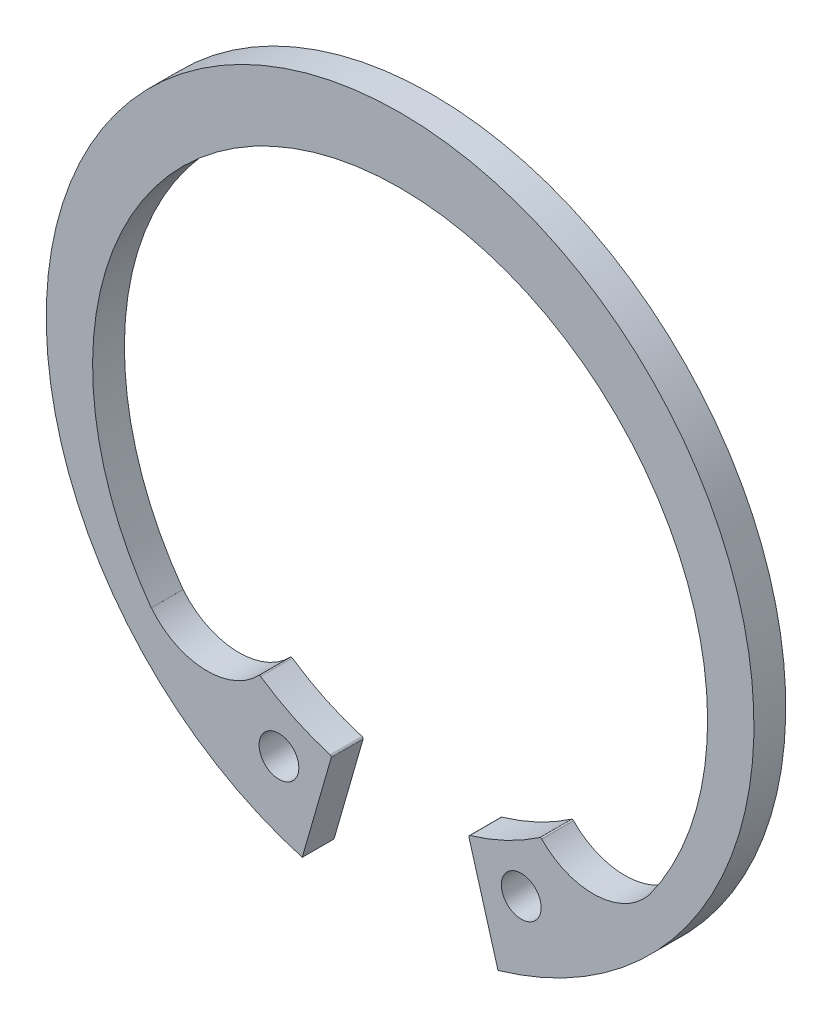
SolidWorks part; units mm, degrees
ref_plane "Plane1" through (0, 0, 0) normal (0, 0, 1) x (1, 0, 0)
ref_plane "Plane2" through (0, 0, 0) normal (0, 1, 0) x (1, 0, 0)
ref_plane "Plane3" through (0, 0, 0) normal (1, 0, 0) x (0, 0, -1)
extrude "Body" add sketch "BodySke" against normal blind 2
sketch "BodySke" plane through (0, 0, 0) normal (0, 0, 1) x (1, 0, 0)
  line L0 (-1.5431, 0) -> (1.5431, 0) construction
  line L1 (0, 0) -> (0, 18.15) construction
  line L2 (6.1547, -21.3818) -> (4.9987, -17.3656)
  line L3 (-6.1547, -21.3818) -> (-4.9987, -17.3656)
  line L4 (0, 0) -> (14.8837, -16.539) construction
  line L5 (0, 0) -> (-14.8837, -16.539) construction
  line L6 (-7.2716, -15.4106) -> (-7.9631, -17.813) construction
  line L7 (7.4097, -15.8905) -> (7.825, -17.3331) construction
  arc A0 (-4.9987, -17.3656) -> (-9.6525, -14.7997) centre (-7.6173, -16.6118) ccw
  arc A1 (9.6525, -14.7997) -> (4.9987, -17.3656) centre (7.6173, -16.6118) ccw
  arc A2 (13.5123, -15.0152) -> (-13.5123, -15.0152) centre (0, -1.1852) ccw construction
  arc A3 (6.1547, -21.3818) -> (-6.1547, -21.3818) centre (0, 0) ccw
  circle A4 centre (7.6173, -16.6118) radius 1.25
  circle A5 centre (-7.6173, -16.6118) radius 1.25
  circle A6 centre (7.6173, -16.6118) radius 2.725 construction
  arc A7 (13.6052, -14.9239) -> (-13.6052, -14.9239) centre (0, -1.1852) ccw
  arc A8 (-7.6173, -16.6118) -> (7.6173, -16.6118) centre (0, 0) ccw construction
  arc A9 (-13.6052, -14.9239) -> (-9.6525, -14.7997) centre (-11.6877, -12.9877) ccw
  arc A10 (9.6525, -14.7997) -> (13.6052, -14.9239) centre (11.6877, -12.9877) ccw
  dimension "GrooveDia" = 44.5
  dimension "TipRad" = 2.725
  dimension "HoleOffsetRad" = 18.275
  dimension "HoleDia" = 2.5
  dimension "FilletRad" = 2.725
  dimension "LargeRad" = 18.15
  dimension "SmallRad" = 20.2
  dimension "SmallAngle" = 83.969
  dimension "GapAngle" = 32.117
sketch "Clipboard" plane through (0, 0, 0) normal (0, 0, 1) x (1, 0, 0)
  line L0 (0, 0) -> (4.1, 0)
  line L1 (0, 0) -> (0, 2.05)
  line L2 (0, 0) -> (0, -6.7)
  circle A0 centre (0, 0) radius 1.25
  circle A1 centre (0, 0) radius 21
  dimension "HoleDia" = 2.5
  dimension "BoreDia" = 42
  dimension "LargeSection" = 4.1
  dimension "SmallSection" = 2.05
  dimension "LugSection" = 6.7
sketch "ModLugSke" plane through (0, 0, 0) normal (0, 0, 1) x (1, 0, 0)
  line L0 (6.1547, -21.3818) -> (4.329, -15.039)
  line L1 (-6.1547, -21.3818) -> (-4.329, -15.039)
  line L2 (12.1328, -9.7262) -> (17.3604, -13.9169) construction
  line L3 (-12.1328, -9.7262) -> (-17.3604, -13.9169) construction
  line L4 (-6.1547, -21.3818) -> (-4.9987, -17.3656) construction
  line L5 (4.9987, -17.3656) -> (6.1547, -21.3818) construction
  line L6 (0, 0) -> (0, -18.0732) construction
  line L7 (15.6421, -12.5394) -> (17.3604, -13.9169)
  line L8 (-17.3604, -13.9169) -> (-15.6421, -12.5394)
  arc A0 (6.1547, -21.3818) -> (17.3604, -13.9169) centre (0, 0) ccw
  arc A1 (-8.7715, -12.8399) -> (-4.3968, -14.9155) centre (0, 0) ccw
  arc A2 (6.1547, -21.3818) -> (-6.1547, -21.3818) centre (0, 0) ccw construction
  arc A3 (9.6525, -14.7997) -> (4.9987, -17.3656) centre (7.6173, -16.6118) ccw construction
  arc A4 (-8.7715, -12.8399) -> (-8.8997, -12.853) centre (-8.8279, -12.9225) ccw
  arc A5 (-15.6421, -12.5394) -> (-8.8997, -12.853) centre (-12.1328, -9.7262) ccw
  arc A6 (13.6052, -14.9239) -> (-13.6052, -14.9239) centre (0, -1.1852) ccw construction
  arc A7 (8.8997, -12.853) -> (15.6421, -12.5394) centre (12.1328, -9.7262) ccw
  arc A8 (4.3968, -14.9155) -> (8.7715, -12.8399) centre (0, 0) ccw
  arc A9 (-17.3604, -13.9169) -> (-6.1547, -21.3818) centre (0, 0) ccw
  circle A10 centre (-7.6173, -16.6118) radius 1.25
  circle A11 centre (-7.6173, -16.6118) radius 1.25 construction
  circle A12 centre (7.6173, -16.6118) radius 1.25
  circle A13 centre (7.6173, -16.6118) radius 1.25 construction
  arc A14 (-4.3968, -14.9155) -> (-4.329, -15.039) centre (-4.4251, -15.0114) cw
  arc A15 (4.3968, -14.9155) -> (4.329, -15.039) centre (4.4251, -15.0114) ccw
  arc A16 (8.7715, -12.8399) -> (8.8997, -12.853) centre (8.8279, -12.9225) cw
  point P43 (4.3014, -14.9432)
  dimension "D1" = 0.1
  dimension "LugAng" = 68.677
extrude "ModLug" add sketch "ModLugSke" against normal through all
sketch "UnlSke" [suppressed] plane through (0, 0, 0) normal (0, 0, 1) x (1, 0, 0)
  line L0 (1.9946, -7.8506) -> (3.2259, -12.6966)
  line L1 (-1.9946, -7.8506) -> (-3.2259, -12.6966)
  line L2 (-3.2259, -12.6966) -> (-2.0191, -7.9469) construction
  line L3 (2.0191, -7.9469) -> (3.2259, -12.6966) construction
  arc A0 (1.9946, -7.8506) -> (-1.9946, -7.8506) centre (0, 0) ccw
  arc A1 (3.2259, -12.6966) -> (-3.2259, -12.6966) centre (0, 0) ccw
  arc A2 (3.2259, -12.6966) -> (-3.2259, -12.6966) centre (0, 0) ccw construction
  circle A4 centre (-4.6101, -9.2107) radius 1
  circle A5 centre (4.6101, -9.2107) radius 1
  circle A6 centre (4.6101, -9.2107) radius 1 construction
  circle A7 centre (-4.6101, -9.2107) radius 1 construction
  arc A8 (2.0902, -7.8257) -> (4.8943, -6.4541) centre (0, 0) ccw construction
extrude "Unlug" [suppressed] add sketch "UnlSke" against normal through all
equation "' \"BoreDia@Clipboard\" = 20"
equation "' \"Thickness@Body\" = 1.5"
equation "' \"GrooveDia@BodySke\" = 21"
equation "' \"LugSection@Clipboard\" = 4.5"
equation "' \"LargeSection@Clipboard\" = 2.4"
equation "' \"HoleDia@Clipboard\" = 2"
equation "' \"BoreDia@Clipboard\" = 25"
equation "' \"GrooveDia@BodySke\" = 26.2"
equation "' \"LugSection@Clipboard\" = 5"
equation "' \"LargeSection@Clipboard\" = 3.1"
equation "\"SmallSection@Clipboard\" = \"LargeSection@Clipboard\" * 0.5"
equation "\"TipRad@BodySke\" = (\"LugSection@Clipboard\" - (\"GrooveDia@BodySke\" / 2  -  \"BoreDia@Clipboard\" / 2 ) ) / 2"
equation "\"HoleOffsetRad@BodySke\" = (\"GrooveDia@BodySke\" / 2) - \"LugSection@Clipboard\"  + \"TipRad@BodySke\""
equation "\"LargeRad@BodySke\" =  \"GrooveDia@BodySke\" / 2 -  \"LargeSection@Clipboard\""
equation "\"SmallRad@BodySke\" =  \"GrooveDia@BodySke\" / 2 -  \"SmallSection@Clipboard\""
equation "\"HoleDia@BodySke\" =  \"HoleDia@Clipboard\""
equation "\"FilletRad@BodySke\" = \"TipRad@BodySke\" * 1.0"
equation "\"GapAngle@BodySke\" = 360 - 0.965 * 360 * ( \"BoreDia@Clipboard\" /  \"GrooveDia@BodySke\")"
equation "\"LugAng@ModLugSke\" = \"GapAngle@BodySke\"  + 2 * 360 * (\"LugSection@Clipboard\" / (\"BoreDia@Clipboard\" * 3.1416))"
